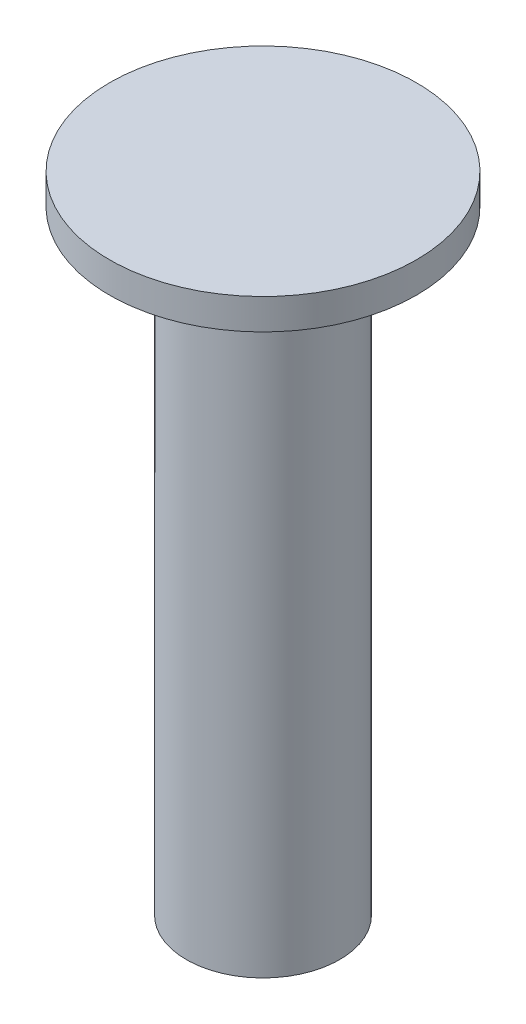
SolidWorks part; units mm, degrees
ref_plane "Plan de face" through (0, 0, 0) normal (0, 0, 1) x (1, 0, 0)
ref_plane "Plan de dessus" through (0, 0, 0) normal (0, 1, 0) x (1, 0, 0)
ref_plane "Plan de droite" through (0, 0, 0) normal (1, 0, 0) x (0, 0, -1)
sketch "Esquisse1" plane through (0, 0, 0) normal (0, 0, 1) x (1, 0, 0)
  line L0 (0, 0) -> (-2.5, 0)
  line L1 (-2.5, 0) -> (-2.5, 20)
  line L2 (-2.5, 20) -> (-5, 20)
  line L3 (-5, 20) -> (-5, 21)
  line L4 (-5, 21) -> (0, 21)
  line L5 (0, 21) -> (0, 0)
revolve "Révolution1" add sketch "Esquisse1" angle 360 about L5
